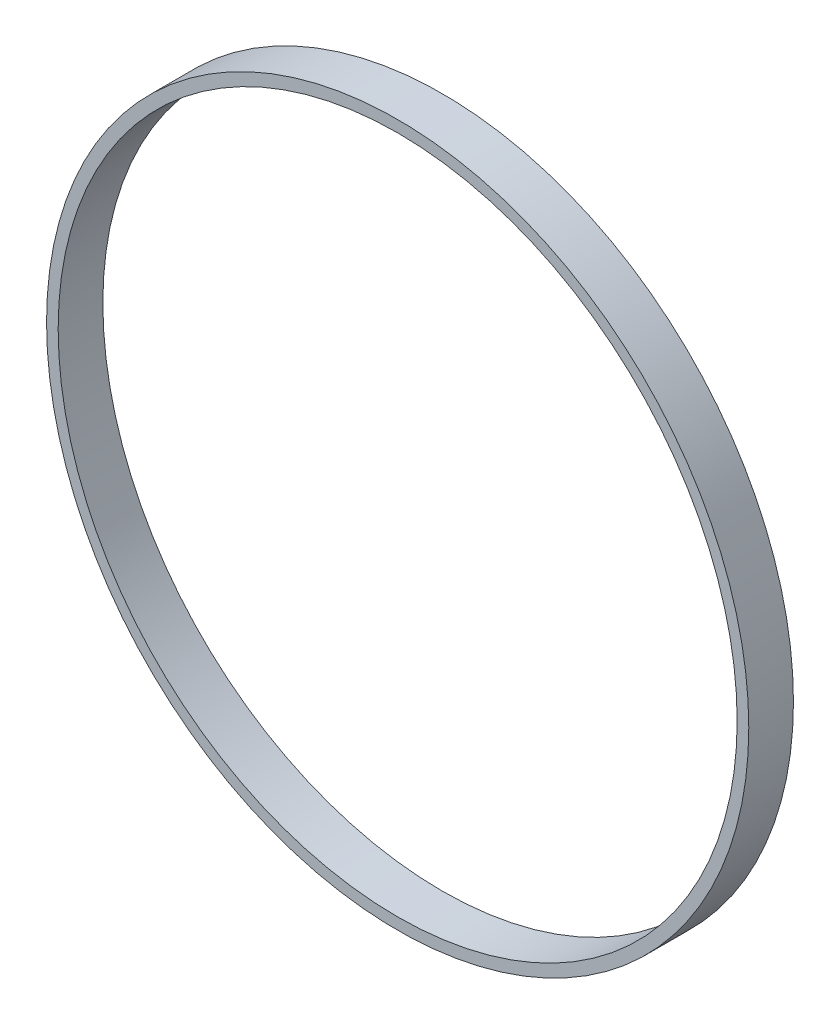
SolidWorks part; units mm, degrees
ref_plane "Front Plane" through (0, 0, 0) normal (0, 0, 1) x (1, 0, 0)
ref_plane "Top Plane" through (0, 0, 0) normal (0, 1, 0) x (1, 0, 0)
ref_plane "Right Plane" through (0, 0, 0) normal (1, 0, 0) x (0, 0, -1)
sketch "Sketch1" plane through (0, 0, 0) normal (0, 0, 1) x (1, 0, 0)
  circle A0 centre (0, 0) radius 76
  circle A1 centre (0, 0) radius 78.6
  dimension "D1" = 152
  dimension "D2" = 157.2
extrude "Boss-Extrude1" add sketch "Sketch1" along normal blind 10
